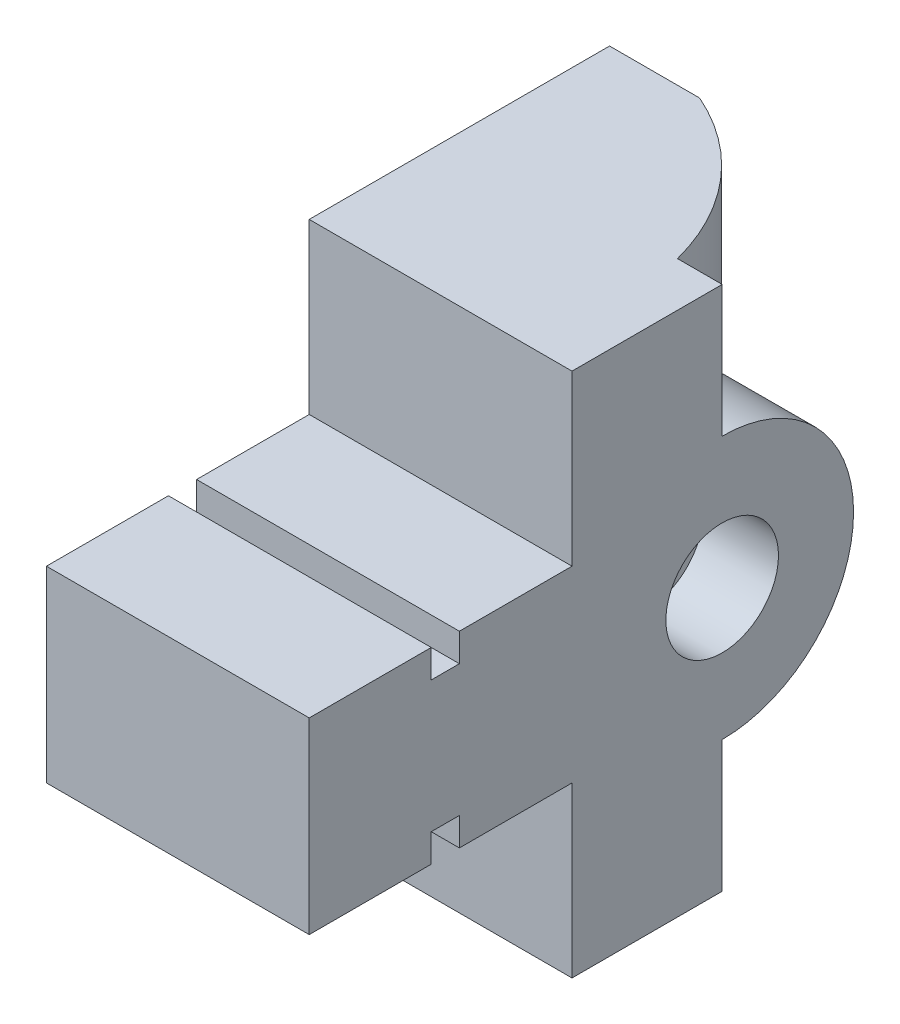
SolidWorks part; units mm, degrees
material "Gray Cast Iron"
ref_plane "Front Plane" through (0, 0, 0) normal (0, 0, 1) x (1, 0, 0)
ref_plane "Top Plane" through (0, 0, 0) normal (0, 1, 0) x (1, 0, 0)
ref_plane "Right Plane" through (0, 0, 0) normal (1, 0, 0) x (0, 0, -1)
sketch "Sketch2" plane through (0, 0, 0) normal (0, 1, 0) x (1, 0, 0)
  line L0 (0, 0) -> (0, 50.8)
  line L1 (0, 0) -> (0, -44.45)
  line L2 (0, -44.45) -> (44.45, -44.45)
  line L3 (44.45, -44.45) -> (44.45, 25.4)
  line L4 (0, 50.8) -> (15.2268, 50.8)
  line L5 (44.45, 25.4) -> (36.8902, 25.4)
  arc A0 (36.8902, 25.4) -> (15.2268, 50.8) centre (0, 15.875) ccw
  point P4 (0, 15.875)
  dimension "D6" = 76.2
  dimension "D1" = 50.8
  dimension "D2" = 44.45
  dimension "D3" = 44.45
  dimension "D4" = 69.85
  dimension "D5" = 34.925
extrude "Boss-Extrude1" add sketch "Sketch2" along normal blind 88.9
sketch "Sketch3" plane through (44.45, 0, 0) normal (1, 0, 0) x (0, 0, -1)
  line L0 (25.4, 88.9) -> (25.4, 0) construction
  line L1 (25.4, 66.675) -> (25.4, 22.225)
  arc A0 (25.4, 22.225) -> (25.4, 66.675) centre (25.4, 44.45) ccw
  dimension "D1" = 44.45
extrude "Boss-Extrude2" add sketch "Sketch3" against normal blind 44.45
sketch "Sketch4" plane through (44.45, 0, 0) normal (1, 0, 0) x (0, 0, -1)
  line L0 (25.4, 88.9) -> (25.4, 0)
  circle A0 centre (25.4, 44.45) radius 9.525
  dimension "D1" = 19.05
extrude "Cut-Extrude1" cut sketch "Sketch4" against normal blind 12.7 contours L0 A0 | L0 A0
sketch "Sketch5" plane through (44.45, 0, 0) normal (1, 0, 0) x (0, 0, -1)
  line L0 (-44.45, 88.9) -> (-44.45, 0) construction
  line L1 (-44.45, 44.45) -> (47.625, 44.45)
  line L2 (-44.45, 88.9) -> (0, 88.9)
  line L3 (-44.45, 88.9) -> (25.4, 88.9) construction
  line L4 (-44.45, 88.9) -> (-44.45, 60.325)
  line L5 (0, 88.9) -> (0, 60.325)
  line L6 (0, 60.325) -> (-19.05, 60.325)
  line L7 (-19.05, 60.325) -> (-19.05, 55.5625)
  line L8 (-19.05, 55.5625) -> (-23.8125, 55.5625)
  line L9 (-23.8125, 55.5625) -> (-23.8125, 60.325)
  line L10 (-23.8125, 60.325) -> (-44.45, 60.325)
  line L11 (-23.8125, 33.3375) -> (-23.8125, 28.575)
  line L12 (-19.05, 33.3375) -> (-23.8125, 33.3375)
  line L13 (-19.05, 28.575) -> (-19.05, 33.3375)
  line L14 (0, 28.575) -> (-19.05, 28.575)
  line L15 (0, 0) -> (0, 28.575)
  line L16 (-44.45, 0) -> (0, 0)
  line L17 (-44.45, 0) -> (-44.45, 28.575)
  line L18 (-23.8125, 28.575) -> (-44.45, 28.575)
  arc A0 (25.4, 22.225) -> (25.4, 66.675) centre (25.4, 44.45) ccw construction
  point P0 (-44.45, 60.325)
  line M11 (-44.45, 0) -> (25.4, 0)
  line M15 (25.4, 88.9) -> (-44.45, 88.9)
  line M16 (-44.45, 88.9) -> (-44.45, 0)
  dimension "D1" = 28.575
  dimension "D2" = 44.45
  dimension "D3" = 28.575
  dimension "D4" = 19.05
  dimension "D5" = 4.7625
  dimension "D6" = 4.7625
  dimension "D7" = 4.7625
extrude "Cut-Extrude2" cut sketch "Sketch5" against normal blind 44.45 contours L10 L9 L8 L7 L6 L5 M15 M16 | L11 L18 L15 L14 L13 L12 M16 M11
